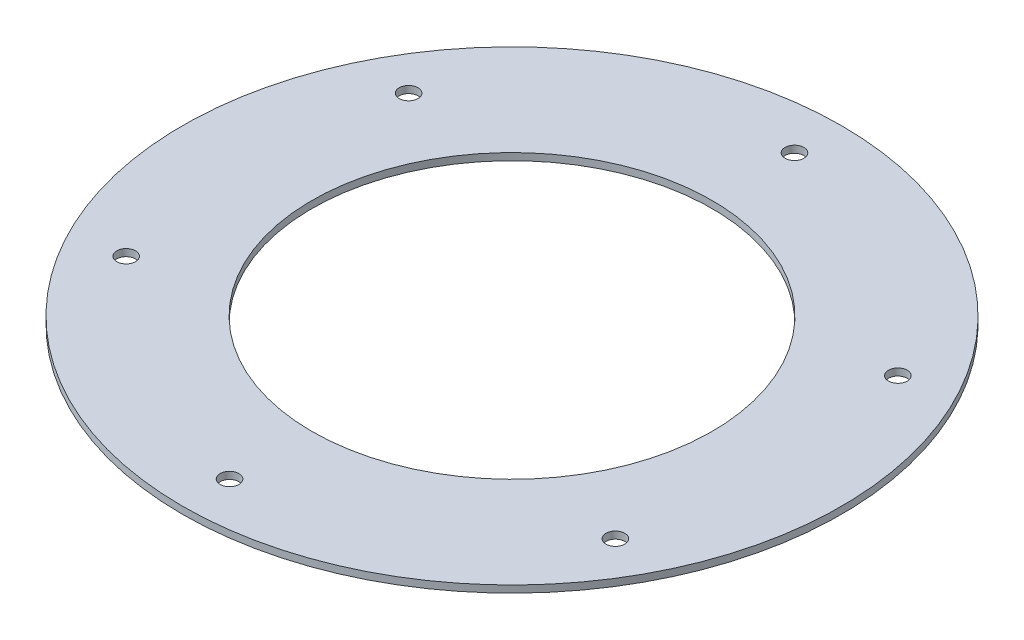
SolidWorks part; units mm, degrees
ref_plane "Alzado" through (0, 0, 0) normal (0, 0, 1) x (1, 0, 0)
ref_plane "Planta" through (0, 0, 0) normal (0, 1, 0) x (1, 0, 0)
ref_plane "Vista lateral" through (0, 0, 0) normal (1, 0, 0) x (0, 0, -1)
sketch "Croquis1" plane through (0, 0, 0) normal (0, 1, 0) x (1, 0, 0)
  circle A0 centre (0, 0) radius 85
  circle A1 centre (0, 0) radius 140
  dimension "D1" = 170
  dimension "D2" = 280
extrude "Saliente-Extruir1" add sketch "Croquis1" along normal blind 3
sketch "Croquis2" plane through (0, 3, 0) normal (0, 1, 0) x (1, 0, 0)
  line L0 (0, 0) -> (0, 156.286) construction
  circle A0 centre (0, 120) radius 4
  circle A1 centre (103.923, 60) radius 4
  circle A2 centre (103.923, -60) radius 4
  circle A3 centre (0, -120) radius 4
  circle A4 centre (-103.923, -60) radius 4
  circle A5 centre (-103.923, 60) radius 4
  point P18 (0, 0)
  dimension "D1" = 8
  dimension "D2" = 120
  dimension "D3" = 6
extrude "Cortar-Extruir1" cut sketch "Croquis2" against normal through all
